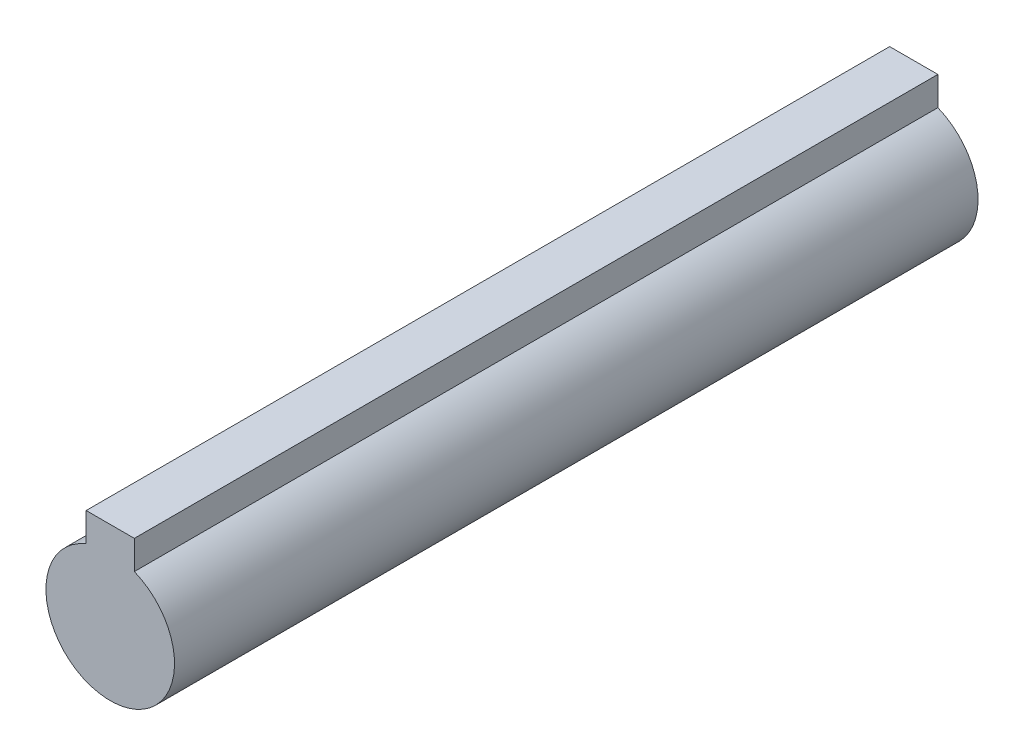
SolidWorks part; units mm, degrees
ref_plane "Front Plane" through (0, 0, 0) normal (0, 0, 1) x (1, 0, 0)
ref_plane "Top Plane" through (0, 0, 0) normal (0, 1, 0) x (1, 0, 0)
ref_plane "Right Plane" through (0, 0, 0) normal (1, 0, 0) x (0, 0, -1)
sketch "Sketch1" plane through (0, 0, 0) normal (0, 0, 1) x (1, 0, 0)
  line L0 (-1.5, 4) -> (1.5, 4) construction
  line L1 (-1.5, 5.5) -> (1.5, 5.5)
  line L2 (-1.5, 5.5) -> (-1.5, 2.5)
  line L3 (-1.5, 2.5) -> (1.5, 2.5)
  line L4 (1.5, 5.5) -> (1.5, 2.5)
  circle A0 centre (0, 0) radius 4
  point P7 (0, 2.5)
  dimension "D1" = 8
  dimension "D2" = 3
  dimension "D3" = 3
extrude "Boss-Extrude1" add sketch "Sketch1" along normal mid plane 50 contours L2 A0 L4 L3 | L4 A0 L2 L3 | L2 L0 L4 L1 | L0 A0 L4 | L0 L2 A0
